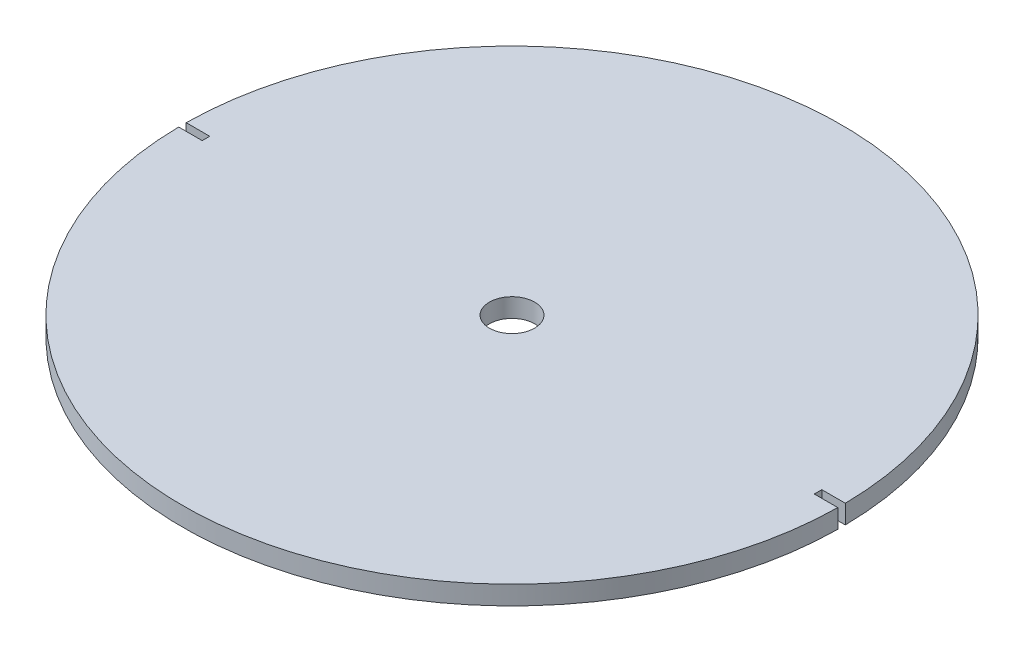
SolidWorks part; units mm, degrees
ref_plane "정면" through (0, 0, 0) normal (0, 0, 1) x (1, 0, 0)
ref_plane "윗면" through (0, 0, 0) normal (0, 1, 0) x (1, 0, 0)
ref_plane "우측면" through (0, 0, 0) normal (1, 0, 0) x (0, 0, -1)
sketch "스케치3" plane through (0, 0, 0) normal (0, 1, 0) x (1, 0, 0)
  circle A1 centre (0, 0) radius 35
  dimension "D1" = 70
extrude "보스-돌출1" add sketch "스케치3" along normal blind 2
sketch "스케치4" plane through (0, 2, 0) normal (0, 1, 0) x (1, 0, 0)
  line L0 (-37.5, 0) -> (-32.5, 0) construction
  line L1 (-37.5, 0.4) -> (-32.5, 0.4)
  line L2 (-37.5, 0.4) -> (-37.5, -0.4)
  line L3 (-37.5, -0.4) -> (-32.5, -0.4)
  line L4 (-32.5, 0.4) -> (-32.5, -0.4)
  line L5 (0, -55) -> (0, 55) construction
  line L6 (-55, 0) -> (55, 0) construction
  line L7 (37.5, -0.4) -> (32.5, -0.4)
  line L8 (32.5, 0.4) -> (32.5, -0.4)
  line L9 (37.5, 0.4) -> (32.5, 0.4)
  line L10 (37.5, 0.4) -> (37.5, -0.4)
  dimension "D1" = 5
  dimension "D2" = 0.8
  dimension "D3" = 37.5
extrude "컷-돌출6" cut sketch "스케치4" against normal through all
sketch "스케치5" plane through (0, 2, 0) normal (0, 1, 0) x (1, 0, 0)
  circle A0 centre (0, 0) radius 2.4
  dimension "D1" = 4.8
extrude "컷-돌출7" cut sketch "스케치5" against normal through all
sketch "스케치6" plane through (0, 0, 0) normal (0, -1, 0) x (1, 0, 0)
  line L0 (1.1, 0) -> (-1.1, 0) construction
  line L1 (-22.0836, 12.75) -> (-22.0836, -12.75)
  line L2 (-22.0836, -12.75) -> (0, -25.5)
  line L3 (0, -25.5) -> (22.0836, -12.75)
  line L4 (22.0836, -12.75) -> (22.0836, 12.75)
  line L5 (22.0836, 12.75) -> (0, 25.5)
  line L6 (0, 25.5) -> (-22.0836, 12.75)
  line L13 (-20.8836, 12.0572) -> (-20.8836, -12.0572)
  line L14 (-20.8836, -12.0572) -> (0, -24.1144)
  line L15 (0, -24.1144) -> (20.8836, -12.0572)
  line L16 (20.8836, -12.0572) -> (20.8836, 12.0572)
  line L17 (20.8836, 12.0572) -> (0, 24.1144)
  line L18 (0, 24.1144) -> (-20.8836, 12.0572)
  circle A0 centre (0, 0) radius 25.5 construction
  dimension "D1" = 51
  dimension "D2" = 1.2
extrude "컷-돌출8" cut sketch "스케치6" against normal blind 1
